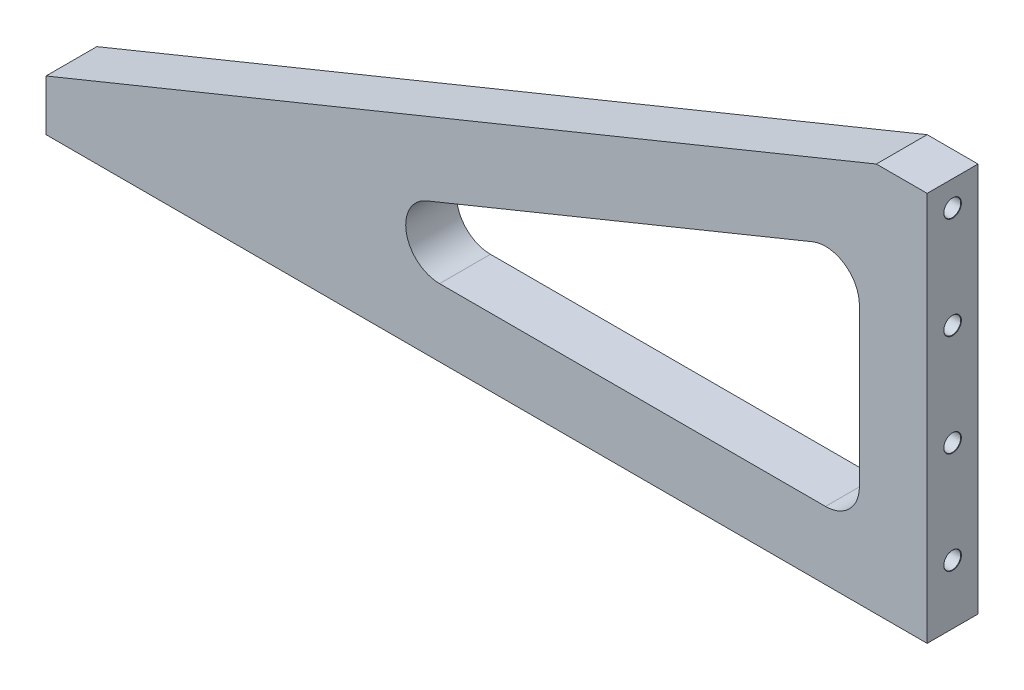
SolidWorks part; units mm, degrees
material "6061-T6 Al"
ref_plane "Front" through (0, 0, 0) normal (0, 0, 1) x (1, 0, 0)
ref_plane "Top" through (0, 0, 0) normal (0, 1, 0) x (1, 0, 0)
ref_plane "Right" through (0, 0, 0) normal (1, 0, 0) x (0, 0, -1)
sketch "Sketch1 w/mock PCB" plane through (0, 0, 0) normal (0, 0, 1) x (1, 0, 0)
  line L0 (-25.4, 99.663) -> (0, 99.663) construction
  line L1 (-19.05, 148.59) -> (-330.2, 21.59)
  line L2 (-19.05, 148.59) -> (0, 148.59)
  line L3 (-330.2, 21.59) -> (-330.2, 2.54)
  line L4 (-330.2, 0) -> (0, 0) construction
  line L6 (0, 148.59) -> (0, 2.54)
  line L7 (-25.4, 99.663) -> (-25.4, 40.64)
  line L8 (-182.7064, 27.94) -> (-38.1, 27.94)
  line L9 (-42.8993, 111.4213) -> (-187.5057, 52.3983)
  line L10 (-38.1, 27.94) -> (-38.1, 2.54) construction
  line L11 (-42.8993, 111.4213) -> (-52.4979, 134.9378) construction
  line L12 (0, 2.54) -> (-330.2, 2.54)
  arc A0 (-25.4, 40.64) -> (-38.1, 27.94) centre (-38.1, 40.64) cw
  arc A2 (-182.7064, 27.94) -> (-187.5057, 52.3983) centre (-182.7064, 40.64) cw
  arc A3 (-42.8993, 111.4213) -> (-25.4, 99.663) centre (-38.1, 99.663) cw
  point P5 (-25.908, 20.828)
  point P6 (25.908, 20.828)
  point P7 (25.908, -20.828)
  point P8 (-25.908, -20.828)
  point P63 (-25.781, -19.05)
  point P64 (25.781, -19.05)
  dimension "D5" = 19.05
  dimension "D7" = 12.7
  dimension "D1" = 330.2
  dimension "D2" = 148.59
  dimension "D3" = 25.4
  dimension "D4" = 2.54
extrude "Boss-Extrude1" add sketch "Sketch1 w/mock PCB" along normal mid plane 19.05
hole_wizard "1/4-20 Tapped Hole3" positions "Sketch7" profile "Sketch6" tap size "1/4-20" standard "ANSI Inch"
sketch "Sketch7" plane through (0, 31.3935, 0.7652) normal (-1, 0, 0) x (0, 0, 1)
  line L6 (-0.7652, -31.3935) -> (-0.7652, -6.6285) construction
  line L11 (-0.7652, 107.6715) -> (-0.7652, 69.5715) construction
  line L12 (-0.7652, 69.5715) -> (-0.7652, 31.4715) construction
  line L13 (-0.7652, 31.4715) -> (-0.7652, -6.6285) construction
  point P57 (-0.7652, 107.6715)
  point P59 (-0.7652, 69.5715)
  point P61 (-0.7652, 31.4715)
  point P63 (-0.7652, -6.6285)
  dimension "D1" = 24.765
  dimension "D2" = 38.1
sketch "Sketch6" plane through (0, 139.065, 0) normal (0, 1, 0) x (0, 0, -1)
  line L0 (0, 0) -> (0, 20.5838)
  line L1 (0, 20.5838) -> (2.5527, 19.05)
  line L2 (2.5527, 19.05) -> (2.5527, 17.78)
  line L3 (2.5527, 17.78) -> (3.175, 17.78)
  line L5 (3.175, 17.78) -> (3.175, 0.127)
  line L6 (3.175, 0.127) -> (3.302, 0)
  line L7 (3.302, 0) -> (0, 0)
  line L8 (-3.175, 0.127) -> (-3.302, 0) construction
  line L10 (0, 20.5838) -> (-2.5527, 19.05) construction
  line L11 (0, -6.35) -> (0, 107.95) construction
  dimension "Tap Drill Dia." = 5.1054
  dimension "Tap Drill Depth" = 19.05
  dimension "Thread Major Dia." = 6.35
  dimension "Thread Depth" = 17.78
  dimension "Near C'Sink Dia." = 6.604
  dimension "Near C'Sink Angle" = 90
  dimension "Drill Angle" = 118
hole_wizard "1/4-20 Tapped Hole2" positions "Sketch9" profile "Sketch8" tap size "1/4-20" standard "ANSI Inch"
sketch "Sketch9" plane through (0, 2.54, 0) normal (0, -1, 0) x (-1, 0, 0)
  line L0 (330.2, 0) -> (317.5, 0) construction
  line L1 (330.2, -9.525) -> (330.2, 9.525) construction
  line L2 (317.5, 0) -> (241.3, 0) construction
  line L3 (241.3, 0) -> (165.1, 0) construction
  line L4 (165.1, 0) -> (88.9, 0) construction
  line L5 (88.9, 0) -> (12.7, 0) construction
  line L6 (12.7, 0) -> (0, 0) construction
  line L7 (0, -9.525) -> (0, 9.525) construction
  point P18 (12.7, 0)
  point P20 (88.9, 0)
  point P22 (165.1, 0)
  point P24 (241.3, 0)
  point P26 (317.5, 0)
  dimension "D1" = 12.7
sketch "Sketch8" plane through (-12.7, 2.54, 0) normal (1, 0, 0) x (0, 0, -1)
  line L0 (0, 0) -> (0, 20.5838)
  line L1 (0, 20.5838) -> (2.5527, 19.05)
  line L2 (2.5527, 19.05) -> (2.5527, 17.78)
  line L3 (2.5527, 17.78) -> (3.175, 17.78)
  line L5 (3.175, 17.78) -> (3.175, 0.127)
  line L6 (3.175, 0.127) -> (3.302, 0)
  line L7 (3.302, 0) -> (0, 0)
  line L8 (-3.175, 0.127) -> (-3.302, 0) construction
  line L10 (0, 20.5838) -> (-2.5527, 19.05) construction
  line L11 (0, -6.35) -> (0, 107.95) construction
  dimension "Tap Drill Dia." = 5.1054
  dimension "Tap Drill Depth" = 19.05
  dimension "Thread Major Dia." = 6.35
  dimension "Thread Depth" = 17.78
  dimension "Near C'Sink Dia." = 6.604
  dimension "Near C'Sink Angle" = 90
  dimension "Drill Angle" = 118
